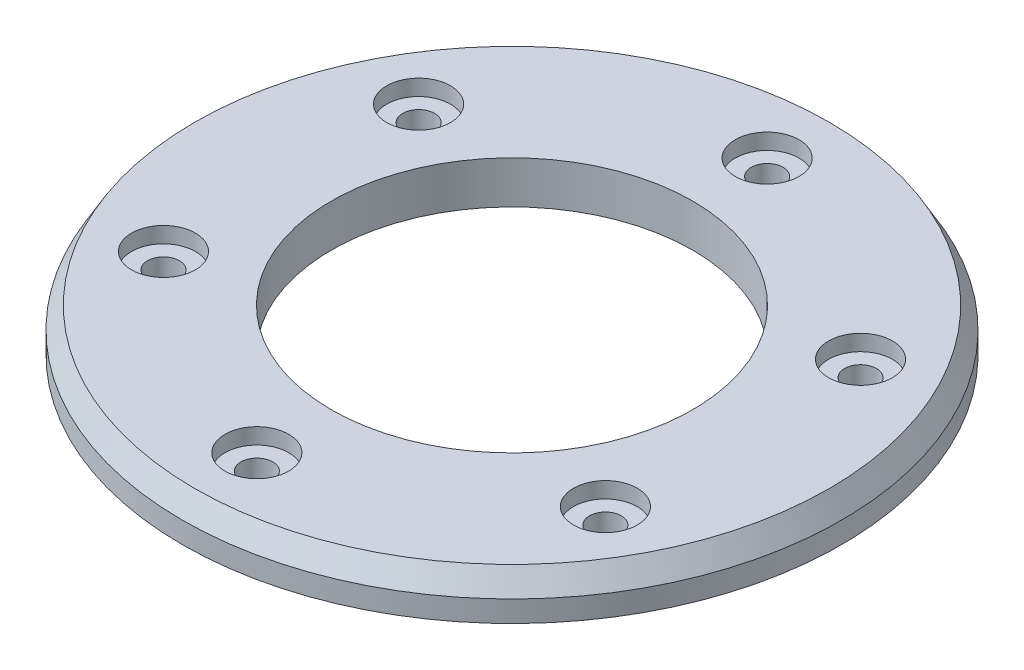
SolidWorks part; units mm, degrees
ref_plane "Front Plane" through (0, 0, 0) normal (0, 0, 1) x (1, 0, 0)
ref_plane "Top Plane" through (0, 0, 0) normal (0, 1, 0) x (1, 0, 0)
ref_plane "Right Plane" through (0, 0, 0) normal (1, 0, 0) x (0, 0, -1)
sketch "Sketch1" plane through (0, 0, 0) normal (0, 1, 0) x (1, 0, 0)
  line L0 (0, 0) -> (0, 24) construction
  circle A0 centre (0, 0) radius 31
  circle A1 centre (0, 0) radius 17
  circle A2 centre (0, 0) radius 24 construction
  circle A3 centre (0, 24) radius 1.5
  circle A4 centre (20.7846, 12) radius 1.5
  circle A5 centre (20.7846, -12) radius 1.5
  circle A6 centre (0, -24) radius 1.5
  circle A7 centre (-20.7846, -12) radius 1.5
  circle A8 centre (-20.7846, 12) radius 1.5
  point P20 (0, 0)
  dimension "D1" = 62
  dimension "D2" = 34
  dimension "D3" = 48
  dimension "D4" = 3
  dimension "D5" = 6
extrude "Boss-Extrude1" add sketch "Sketch1" along normal blind 4
sketch "Sketch2" plane through (0, 4, 0) normal (0, 1, 0) x (1, 0, 0)
  line L0 (0, 0) -> (0, 24) construction
  circle A0 centre (0, 24) radius 3
  circle A6 centre (20.7846, 12) radius 3
  circle A7 centre (20.7846, -12) radius 3
  circle A8 centre (0, -24) radius 3
  circle A9 centre (-20.7846, -12) radius 3
  circle A10 centre (-20.7846, 12) radius 3
  point P18 (0.433, -0.25)
  point P19 (0, 0)
  dimension "D1" = 6
extrude "Cut-Extrude1" cut sketch "Sketch2" against normal blind 1.5
chamfer "Chamfer1" distance 2 angle 30 1 edges at (0, 4, 31)
